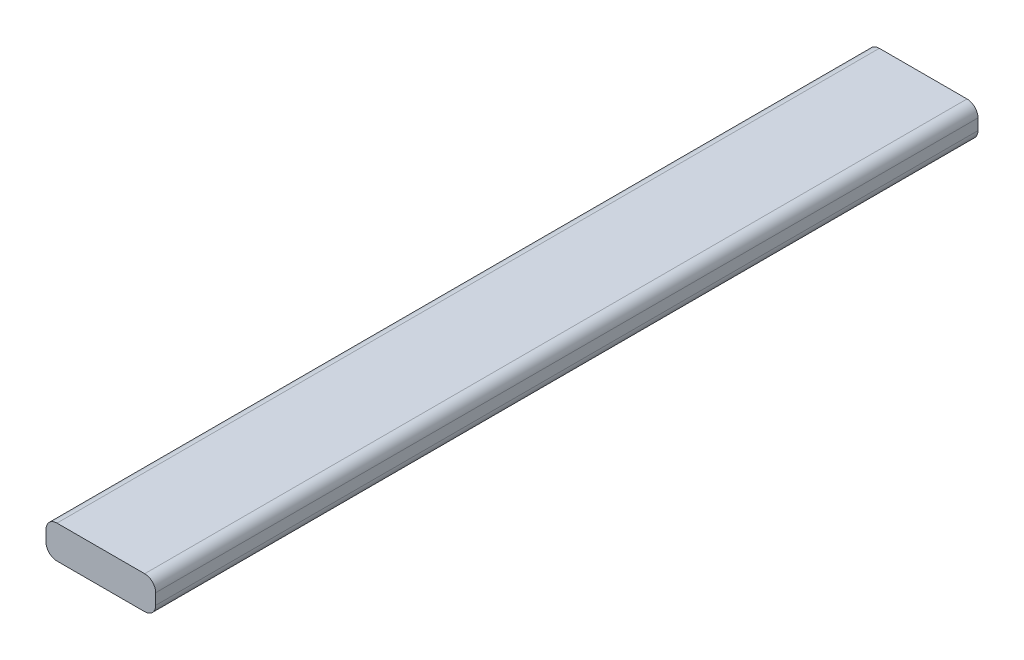
SolidWorks part; units mm, degrees
ref_plane "Plan de face" through (0, 0, 0) normal (0, 0, 1) x (1, 0, 0)
ref_plane "Plan de dessus" through (0, 0, 0) normal (0, 1, 0) x (1, 0, 0)
ref_plane "Plan de droite" through (0, 0, 0) normal (1, 0, 0) x (0, 0, -1)
sketch "Esquisse1" plane through (0, 0, 0) normal (0, 0, 1) x (1, 0, 0)
  line L1 (-4, 1.5) -> (4, 1.5)
  line L2 (-5, 0.5) -> (-5, -0.5)
  line L3 (-4, -1.5) -> (4, -1.5)
  line L4 (5, 0.5) -> (5, -0.5)
  arc A0 (4, 1.5) -> (5, 0.5) centre (4, 0.5) cw
  arc A1 (4, -1.5) -> (5, -0.5) centre (4, -0.5) ccw
  arc A2 (-5, -0.5) -> (-4, -1.5) centre (-4, -0.5) ccw
  arc A3 (-4, 1.5) -> (-5, 0.5) centre (-4, 0.5) ccw
  point P4 (-5, 0)
  point P5 (0, 1.5)
  point P11 (5, 1.5)
  point P16 (-5, -1.5)
  point P19 (-5, 1.5)
  dimension "D3" = 1
  dimension "D1" = 10
  dimension "D2" = 3
extrude "Boss.-Extru.1" add sketch "Esquisse1" along normal blind 75
